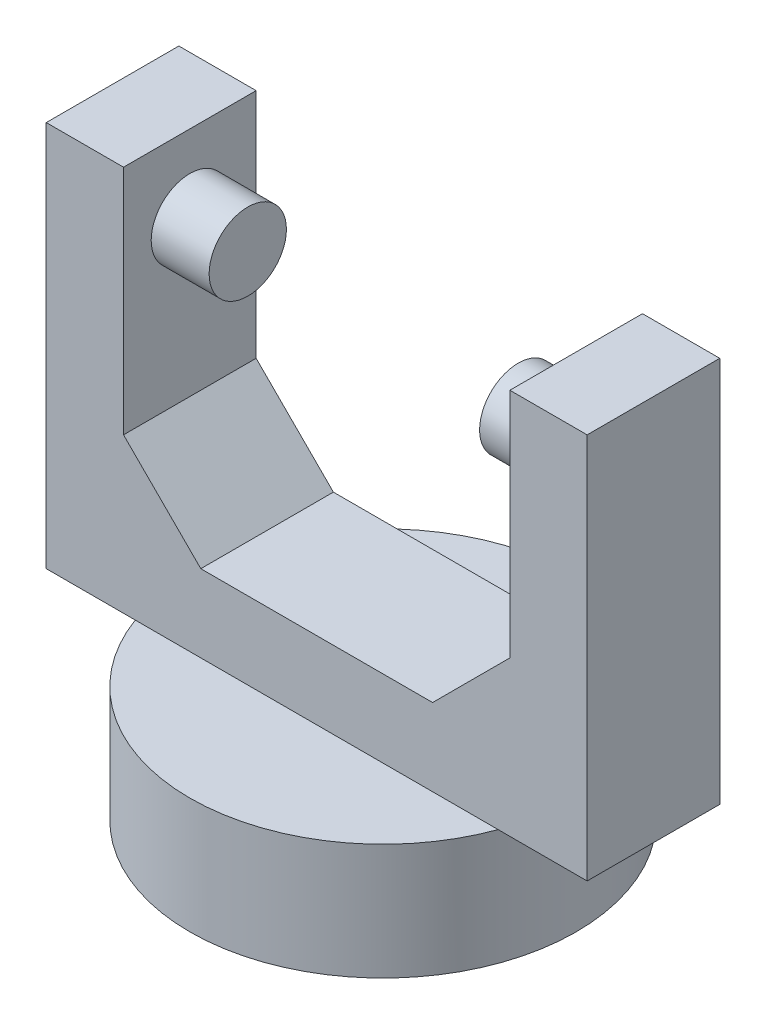
SolidWorks part; units mm, degrees
ref_plane "Front Plane" through (0, 0, 0) normal (0, 0, 1) x (1, 0, 0)
ref_plane "Top Plane" through (0, 0, 0) normal (0, 1, 0) x (1, 0, 0)
ref_plane "Right Plane" through (0, 0, 0) normal (1, 0, 0) x (0, 0, -1)
sketch "Sketch1" plane through (0, 0, 0) normal (0, 1, 0) x (1, 0, 0)
  circle A0 centre (0, 0) radius 12.5
  dimension "D1" = 25
extrude "Boss-Extrude1" add sketch "Sketch1" along normal blind 7.5
sketch "Sketch2" plane through (0, 7.5, 0) normal (0, 1, 0) x (1, 0, 0)
  line L1 (-17.5, 4.2904) -> (17.5, 4.2904)
  line L2 (-17.5, 4.2904) -> (-17.5, -4.2904)
  line L3 (-17.5, -4.2904) -> (17.5, -4.2904)
  line L4 (17.5, 4.2904) -> (17.5, -4.2904)
  point P4 (17.5, 0)
  point P6 (0, 4.2904)
  dimension "D1" = 35
  dimension "D3" = 8.5808
extrude "Boss-Extrude2" add sketch "Sketch2" along normal blind 25
sketch "Sketch3" plane through (0, 32.5, 0) normal (0, 1, 0) x (1, 0, 0)
  line L0 (17.5, 4.2904) -> (-17.5, 4.2904) construction
  line L1 (-12.5, 4.2904) -> (12.5, 4.2904)
  line L2 (-12.5, 4.2904) -> (-12.5, -4.2904)
  line L3 (-12.5, -4.2904) -> (12.5, -4.2904)
  line L4 (12.5, 4.2904) -> (12.5, -4.2904)
  line L5 (-17.5, -4.2904) -> (17.5, -4.2904) construction
  line L6 (17.5, -4.2904) -> (17.5, 4.2904) construction
  line L7 (-17.5, 4.2904) -> (-17.5, -4.2904) construction
  dimension "D1" = 5
  dimension "D2" = 5
extrude "Cut-Extrude1" cut sketch "Sketch3" against normal blind 20
sketch "Sketch4" plane through (-12.5, 0, 0) normal (1, 0, 0) x (0, 0, -1)
  line L0 (4.2904, 12.5) -> (-4.2904, 12.5) construction
  line L1 (4.2904, 32.5) -> (-4.2904, 32.5) construction
  circle A0 centre (0, 27.5) radius 2.5
  point P8 (0, 32.5)
  dimension "D1" = 5
  dimension "D2" = 15
extrude "Boss-Extrude3" add sketch "Sketch4" along normal blind 3.75
sketch "Sketch5" plane through (12.5, 0, 0) normal (-1, 0, 0) x (0, 0, 1)
  circle A0 centre (0, 27.5) radius 2.5
  circle A1 centre (0, 27.5) radius 2.5 construction
  dimension "D1" = 5
extrude "Boss-Extrude4" add sketch "Sketch5" along normal blind 3.75
chamfer "Chamfer1" distance 5 angle 45 1 edges at (-12.5, 12.5, 0)
chamfer "Chamfer2" distance 5 angle 45 1 edges at (12.5, 12.5, 0)
